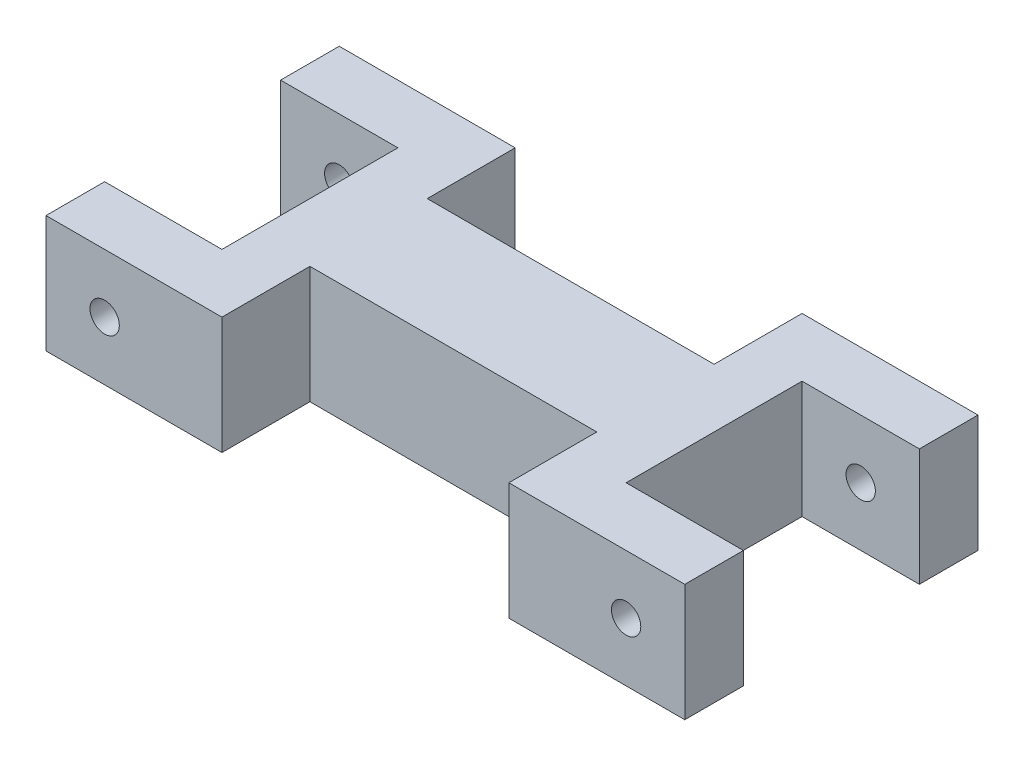
SolidWorks part; units mm, degrees
ref_plane "Front Plane" through (0, 0, 0) normal (0, 0, 1) x (1, 0, 0)
ref_plane "Top Plane" through (0, 0, 0) normal (0, 1, 0) x (1, 0, 0)
ref_plane "Right Plane" through (0, 0, 0) normal (1, 0, 0) x (0, 0, -1)
sketch "Sketch1" plane through (0, 0, 0) normal (0, 1, 0) x (1, 0, 0)
  line L0 (0, 0) -> (8195.2033, 0) construction
  line L1 (0, 0) -> (0, 8195.2033) construction
  line L2 (0, 9.525) -> (-12.7, 9.525)
  line L3 (0, -9.525) -> (-12.7, -9.525)
  line L4 (-12.7, 9.525) -> (-12.7, 15.875)
  line L5 (-12.7, -9.525) -> (-12.7, -15.875)
  line L6 (-12.7, 15.875) -> (6.35, 15.875)
  line L7 (-12.7, -15.875) -> (6.35, -15.875)
  line L8 (6.35, 15.875) -> (6.35, 6.35)
  line L9 (6.35, -15.875) -> (6.35, -6.35)
  line L10 (6.35, 6.35) -> (37.4109, 6.35)
  line L11 (6.35, -6.35) -> (37.4109, -6.35)
  line L12 (37.4109, 6.35) -> (37.4109, 15.875)
  line L13 (37.4109, -6.35) -> (37.4109, -15.875)
  line L14 (37.4109, 15.875) -> (56.4609, 15.875)
  line L15 (37.4109, -15.875) -> (56.4609, -15.875)
  line L16 (56.4609, 15.875) -> (56.4609, 9.525)
  line L17 (56.4609, -15.875) -> (56.4609, -9.525)
  line L18 (56.4609, 9.525) -> (43.7609, 9.525)
  line L19 (56.4609, -9.525) -> (43.7609, -9.525)
  line L20 (0, 9.525) -> (0, -9.525)
  line L21 (43.7609, 9.525) -> (43.7609, -9.525)
  point P6 (0, 0)
  dimension "D3" = 69.1609
  dimension "D4" = 19.05
  dimension "D5" = 12.7
  dimension "D6" = 12.7
  dimension "D7" = 6.35
  dimension "D8" = 6.35
extrude "Boss-Extrude1" add sketch "Sketch1" along normal blind 12.7
sketch "Sketch2" plane through (0, 0, 15.875) normal (0, 0, 1) x (1, 0, 0)
  line L0 (-12.7, 6.35) -> (-6.35, 6.35) construction
  line L1 (21.8805, 0) -> (21.8805, 50000) construction
  line L2 (-6.35, 6.35) -> (21.8805, 6.35) construction
  line L3 (21.8805, 6.35) -> (50.1109, 6.35) construction
  line L4 (-12.7, 0) -> (6.35, 0)
  line L5 (6.35, 0) -> (6.35, 12.7)
  line L6 (6.35, 12.7) -> (-12.7, 12.7)
  line L7 (-12.7, 12.7) -> (-12.7, 0)
  line L8 (-12.7, 0) -> (6.35, 0)
  line L9 (6.35, 0) -> (6.35, 12.7)
  line L10 (6.35, 12.7) -> (-12.7, 12.7)
  line L11 (-12.7, 12.7) -> (-12.7, 0)
  line L12 (6.35, 0) -> (37.4109, 0)
  line L13 (37.4109, 0) -> (37.4109, 12.7)
  line L14 (37.4109, 12.7) -> (6.35, 12.7)
  line L15 (6.35, 12.7) -> (6.35, 0)
  line L16 (6.35, 0) -> (37.4109, 0)
  line L17 (37.4109, 0) -> (37.4109, 12.7)
  line L18 (37.4109, 12.7) -> (6.35, 12.7)
  line L19 (6.35, 12.7) -> (6.35, 0)
  line L20 (37.4109, 0) -> (56.4609, 0)
  line L21 (56.4609, 0) -> (56.4609, 12.7)
  line L22 (56.4609, 12.7) -> (37.4109, 12.7)
  line L23 (37.4109, 12.7) -> (37.4109, 0)
  line L24 (37.4109, 0) -> (56.4609, 0)
  line L25 (56.4609, 0) -> (56.4609, 12.7)
  line L26 (56.4609, 12.7) -> (37.4109, 12.7)
  line L27 (37.4109, 12.7) -> (37.4109, 0)
  line L28 (50.1109, 6.35) -> (56.4609, 6.35) construction
  circle A0 centre (-6.35, 6.35) radius 1.5875
  circle A1 centre (50.1109, 6.35) radius 1.5875
  point P14 (21.8805, 0)
  dimension "D4" = 3.175
  dimension "D5" = 6.35
  dimension "D1" = 0
  dimension "D2" = 0
  dimension "D3" = 0
extrude "Cut-Extrude1" cut sketch "Sketch2" against normal through all contours A1 | A0
